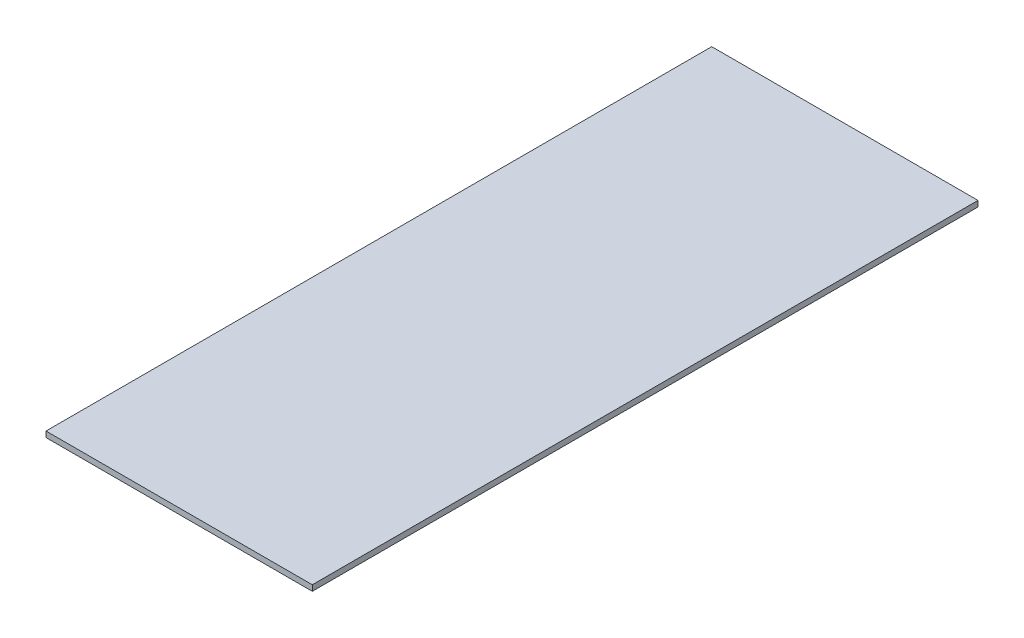
SolidWorks part; units mm, degrees
ref_plane "Front Plane" through (0, 0, 0) normal (0, 0, 1) x (1, 0, 0)
ref_plane "Top Plane" through (0, 0, 0) normal (0, 1, 0) x (1, 0, 0)
ref_plane "Right Plane" through (0, 0, 0) normal (1, 0, 0) x (0, 0, -1)
sketch "Sketch2" plane through (0, 0, 0) normal (0, 1, 0) x (1, 0, 0)
  line L1 (0, 0) -> (140, 0)
  line L2 (0, 0) -> (0, 350)
  line L3 (0, 350) -> (140, 350)
  line L4 (140, 0) -> (140, 350)
  dimension "D1" = 350
  dimension "D2" = 140
extrude "Boss-Extrude1" add sketch "Sketch2" along normal blind 3
